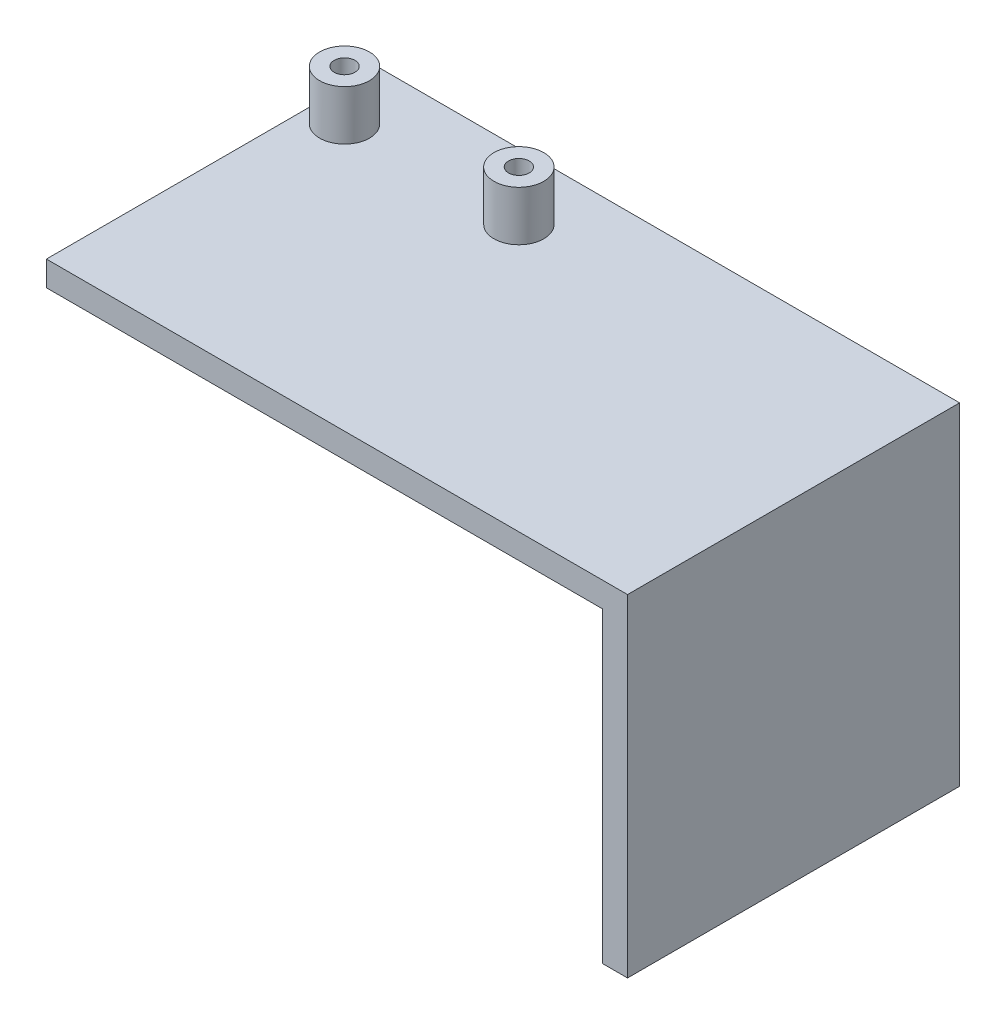
SolidWorks part; units mm, degrees
ref_plane "Front Plane" through (0, 0, 0) normal (0, 0, 1) x (1, 0, 0)
ref_plane "Top Plane" through (0, 0, 0) normal (0, 1, 0) x (1, 0, 0)
ref_plane "Right Plane" through (0, 0, 0) normal (1, 0, 0) x (0, 0, -1)
sketch "Sketch1" plane through (0, 0, 0) normal (0, 1, 0) x (1, 0, 0)
  line L1 (-35, -20) -> (35, -20)
  line L2 (-35, -20) -> (-35, 20)
  line L3 (-35, 20) -> (35, 20)
  line L4 (35, -20) -> (35, 20)
  line L5 (-35, -20) -> (35, 20) construction
  line L6 (-35, 20) -> (35, -20) construction
  point P0 (0, 0)
extrude "Boss-Extrude1" add sketch "Sketch1" along normal blind 40
sketch "Sketch2" plane through (-35, 0, 0) normal (-1, 0, 0) x (0, 0, 1)
  line L0 (20, 40) -> (20, 0) construction
  line L1 (-20, 0) -> (20, 0)
  line L2 (-20, 0) -> (-20, 37)
  line L3 (-20, 37) -> (20, 37)
  line L4 (20, 0) -> (20, 37)
extrude "Cut-Extrude1" cut sketch "Sketch2" against normal blind 67
sketch "Sketch4" plane through (0, 40, 0) normal (0, 1, 0) x (1, 0, 0)
  line L0 (0, 0) -> (0, 12) construction
  line L1 (0, 12) -> (0, 9.1952) construction
  line L2 (0, 12) -> (-42.4281, 12) construction
  circle A0 centre (-31.1498, 12.0628) radius 3
  circle A1 centre (-10.1498, 12.0628) radius 3
extrude "Boss-Extrude2" add sketch "Sketch4" along normal blind 6
sketch "Sketch9" plane through (0, 46, 0) normal (0, 1, 0) x (1, 0, 0)
  point P0 (-10.1498, 12.0628)
  point P1 (-31.1498, 12.0628)
hole_wizard "Tap Drill for M3x0.5 Tap2" positions "Sketch10" profile "Sketch11" hole size "M3x0.5" standard "ANSI Metric"
sketch "Sketch10" plane through (0, 46, 0) normal (0, 1, 0) x (1, 0, 0)
  point P0 (-31.1498, 12.0628)
  point P3 (-10.1498, 12.0628)
sketch "Sketch11" plane through (-31.1498, 46, -12.0628) normal (1, 0, 0) x (0, 0, 1)
  line L0 (0, 0) -> (0, 6.7511)
  line L1 (0, 6.7511) -> (1.25, 6)
  line L2 (1.25, 6) -> (1.25, 0)
  line L5 (1.25, 0) -> (0, 0)
  line L10 (0, 6.7511) -> (-1.25, 6) construction
  line L11 (0, -6.35) -> (0, 107.95) construction
  dimension "Hole Dia." = 2.5
  dimension "Hole Depth" = 6
  dimension "Drill Angle" = 118
